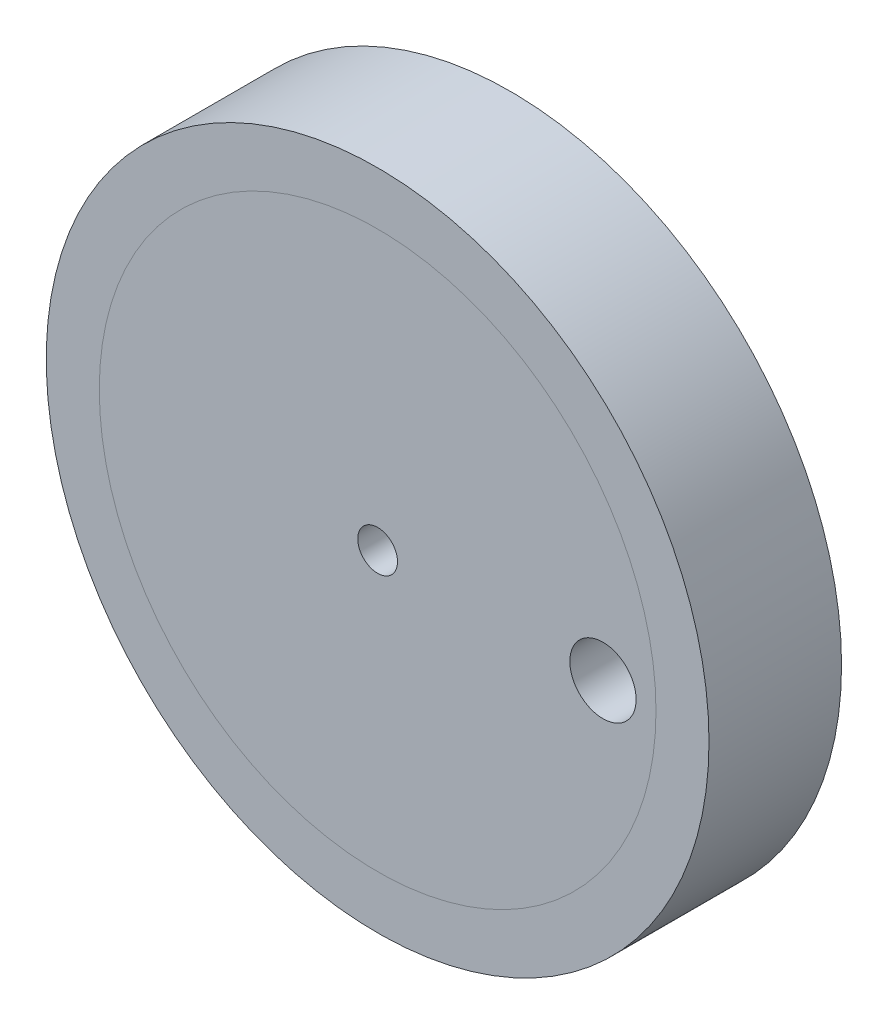
SolidWorks part; units mm, degrees
ref_plane "Спереди" through (0, 0, 0) normal (0, 0, 1) x (1, 0, 0)
ref_plane "Сверху" through (0, 0, 0) normal (0, 1, 0) x (1, 0, 0)
ref_plane "Справа" through (0, 0, 0) normal (1, 0, 0) x (0, 0, -1)
other "Configuration Table"
sketch "Sketch1" plane through (0, 0, 0) normal (0, 0, 1) x (1, 0, 0)
  circle A0 centre (-26.1266, 11.2615) radius 25
  dimension "D1" = 50
extrude "Boss-Extrude1" add sketch "Sketch1" along normal blind 10 contours A0
ref_plane "Plane1" through (0, 0, 10) normal (0, 0, 1) x (1, 0, 0)
sketch "Sketch3" plane through (0, 0, 10) normal (0, 0, 1) x (1, 0, 0)
  circle A0 centre (-26.1266, 11.2615) radius 21
  point P0 (-26.1266, 11.2615)
  dimension "D1" = 42
extrude "Boss-Extrude2" add sketch "Sketch3" against normal blind 10.0001 separate body
combine bodies "Combine1" operation type subtract main body 103 bodies to subtract 104
ref_plane "Plane2" through (0, 0, 0) normal (0, 0, -1) x (-1, 0, 0)
sketch "Sketch4" plane through (0, 0, 0) normal (0, 0, -1) x (-1, 0, 0)
  circle A0 centre (26.1266, 11.2615) radius 21
  circle A1 centre (26.1266, 11.2615) radius 1.5
  circle A2 centre (9.1266, 11.2615) radius 2.5
  point P0 (26.1266, 11.2615)
  dimension "D1" = 3
  dimension "D2" = 5
  dimension "D3" = 17
extrude "Boss-Extrude3" add sketch "Sketch4" against normal up to surface (10 mm away) separate body contours A0
ref_plane "Plane4" through (0, 0, 0) normal (0, 0, -1) x (-1, 0, 0)
